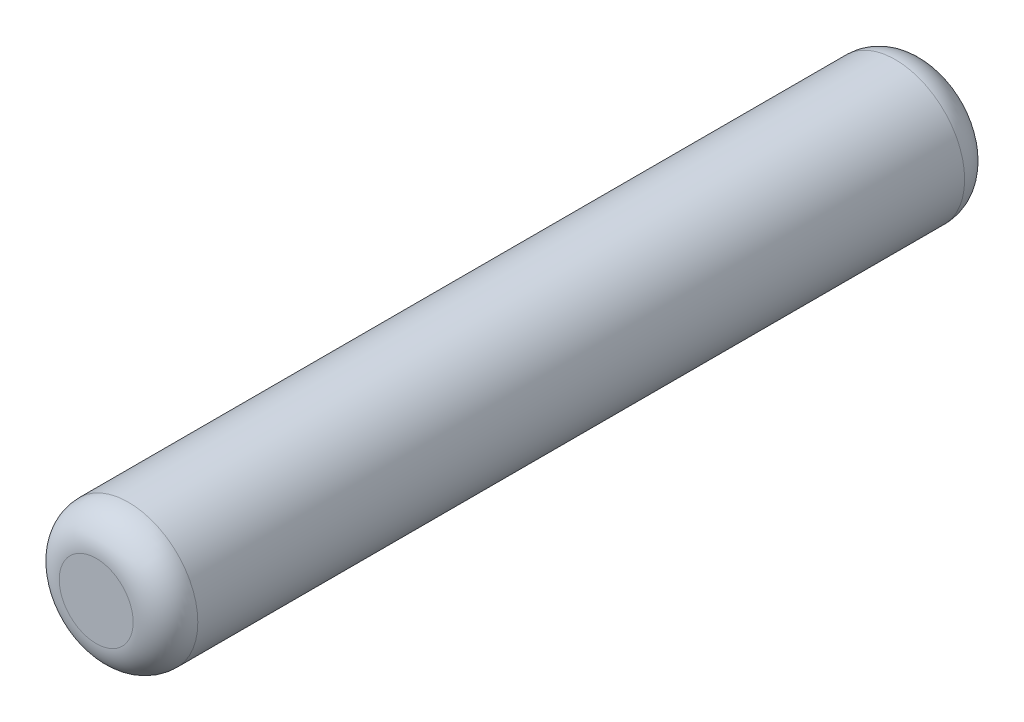
SolidWorks part; units mm, degrees
ref_plane "Front" through (0, 0, 0) normal (0, 0, 1) x (1, 0, 0)
ref_plane "Top" through (0, 0, 0) normal (0, 1, 0) x (1, 0, 0)
ref_plane "Right" through (0, 0, 0) normal (1, 0, 0) x (0, 0, -1)
sketch "Sketch1" plane through (0, 0, 0) normal (0, 0, 1) x (1, 0, 0)
  circle A0 centre (0, 0) radius 0.75
  dimension "D1" = 1.5
extrude "Boss-Extrude1" add sketch "Sketch1" along normal mid plane 9
fillet "Fillet1" radius 0.35 2 edges at (0.75, 0, -4.5) (0.75, 0, 4.5)
